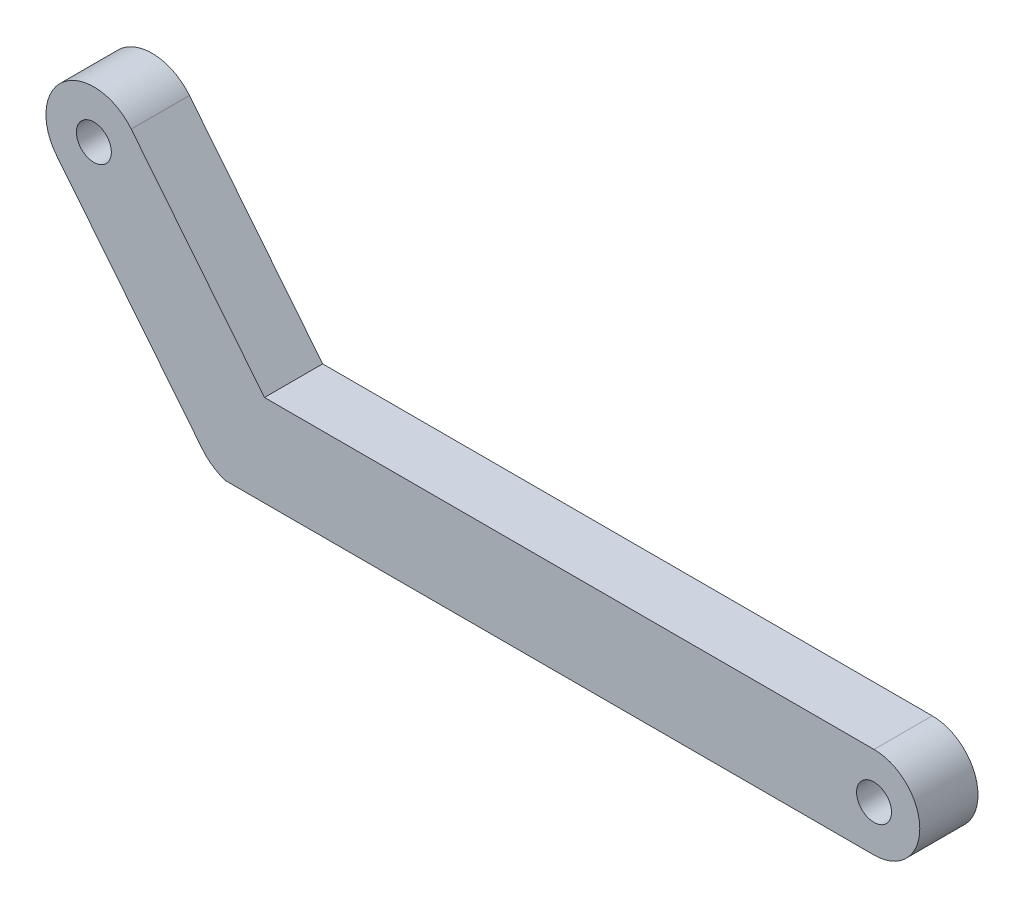
SolidWorks part; units mm, degrees
ref_plane "Front Plane" through (0, 0, 0) normal (0, 0, 1) x (1, 0, 0)
ref_plane "Top Plane" through (0, 0, 0) normal (0, 1, 0) x (1, 0, 0)
ref_plane "Right Plane" through (0, 0, 0) normal (1, 0, 0) x (0, 0, -1)
sketch "Sketch1" plane through (0, 0, 0) normal (0, 0, 1) x (1, 0, 0)
  line L0 (0, 0) -> (65.3421, 0) construction
  line L3 (0, 3.9281) -> (65.3421, 3.9281)
  line L4 (0, -3.9281) -> (65.3421, -3.9281)
  line L5 (10.8692, 0) -> (-1.6579, 15.5907) construction
  line L6 (7.6606, -2.5781) -> (-4.8665, 13.0127)
  line L7 (14.0777, 2.5781) -> (1.5506, 18.1688)
  line L8 (-1.6579, 15.5907) -> (65.3421, 0)
  arc A4 (0, 3.9281) -> (0, -3.9281) centre (0, 0) ccw
  arc A5 (65.3421, -3.9281) -> (65.3421, 3.9281) centre (65.3421, 0) ccw
  arc A6 (7.6606, -2.5781) -> (14.0777, 2.5781) centre (10.8692, 0) ccw
  arc A7 (1.5506, 18.1688) -> (-4.8665, 13.0127) centre (-1.6579, 15.5907) ccw
  circle A8 centre (-1.6579, 15.5907) radius 1.5
  circle A9 centre (65.3421, 0) radius 1.5
  point P3 (32.671, 0)
  point P10 (4.6056, 7.7954)
  dimension "D3" = 3
  dimension "D4" = 3
  dimension "D1" = 15.5907
  dimension "D2" = 20
  dimension "D5" = 67
extrude "Boss-Extrude2" add sketch "Sketch1" along normal blind 5 contours L7 A7 L6 L3 A8 | A6 L4 A5 L3 L7 A9 | L6 A6 L4 L7 L3
